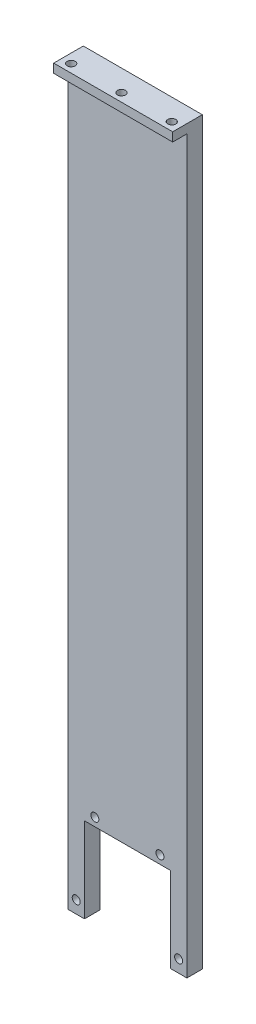
SolidWorks part; units mm, degrees
material "6061 Alloy"
ref_plane "Front Plane" through (0, 0, 0) normal (0, 0, 1) x (1, 0, 0)
ref_plane "Top Plane" through (0, 0, 0) normal (0, 1, 0) x (1, 0, 0)
ref_plane "Right Plane" through (0, 0, 0) normal (1, 0, 0) x (0, 0, -1)
sketch "Sketch1" plane through (0, 0, 0) normal (0, 0, 1) x (1, 0, 0)
  line L1 (-20.1, -125) -> (20.1, -125)
  line L2 (-20.1, -125) -> (-20.1, 125)
  line L3 (-20.1, 125) -> (20.1, 125)
  line L4 (20.1, -125) -> (20.1, 125)
  line L5 (-20.1, -125) -> (20.1, 125) construction
  line L6 (-20.1, 125) -> (20.1, -125) construction
  point P0 (0, 0)
  dimension "D1" = 40.2
  dimension "D2" = 250
extrude "Boss-Extrude1" add sketch "Sketch1" along normal blind 10
sketch "Sketch3" plane through (0, 0, 10) normal (0, 0, 1) x (1, 0, 0)
  line L0 (-20.1, -125) -> (20.1, -125) construction
  line L1 (-14.5, -96.3) -> (14.5, -96.3)
  line L2 (-14.5, -96.3) -> (-14.5, -125)
  line L3 (-14.5, -125) -> (14.5, -125)
  line L4 (14.5, -96.3) -> (14.5, -125)
  line L5 (-14.5, -96.3) -> (14.5, -125) construction
  line L6 (-14.5, -125) -> (14.5, -96.3) construction
  point P0 (0, -110.65)
  dimension "D1" = 29
  dimension "D2" = 28.7
sketch "Sketch2" plane through (0, 0, 10) normal (0, 0, 1) x (1, 0, 0)
  line L2 (-11, -93.5) -> (11, -93.5) construction
  line L3 (-17.3, -93.5) -> (17.3, -93.5) construction
  line L4 (-17.3, -93.5) -> (-17.3, -120.8) construction
  line L5 (-17.3, -120.8) -> (17.3, -120.8) construction
  line L6 (17.3, -93.5) -> (17.3, -120.8) construction
  line L7 (-17.3, -93.5) -> (17.3, -120.8) construction
  line L8 (-17.3, -120.8) -> (17.3, -93.5) construction
  line L9 (-20.1, -125) -> (20.1, -125) construction
  circle A0 centre (17.3, -120.8) radius 1.35
  circle A1 centre (11, -93.5) radius 1.35
  circle A2 centre (-17.3, -120.8) radius 1.35
  circle A3 centre (-11, -93.5) radius 1.35
  point P11 (0, -107.15)
  point P12 (0, -93.5)
  dimension "D1" = 4.2
  dimension "D2" = 2.7
  dimension "D3" = 22
  dimension "D4" = 27.3
  dimension "D5" = 34.6
sketch "Sketch4" plane through (0, 0, 10) normal (0, 0, 1) x (1, 0, 0)
  line L0 (-20.1, 125) -> (-20.1, -125) construction
  line L1 (-20.1, 122) -> (20.1, 122)
  line L2 (-20.1, 122) -> (-20.1, -125)
  line L3 (-20.1, -125) -> (20.1, -125)
  line L4 (20.1, 122) -> (20.1, -125)
  line L5 (-20.1, 122) -> (20.1, -125) construction
  line L6 (-20.1, -125) -> (20.1, 122) construction
  line L7 (20.1, 125) -> (-20.1, 125) construction
  point P0 (0, -1.5)
  dimension "D1" = 3
extrude "Cut-Extrude1" cut sketch "Sketch4" against normal blind 4.8
extrude "Cut-Extrude2" cut sketch "Sketch3" against normal through all
extrude "Cut-Extrude3" cut sketch "Sketch2" against normal through all
sketch "Sketch6" plane through (0, 125, 0) normal (0, 1, 0) x (-1, 0, 0)
  line L0 (17, 7.2) -> (-17, 7.2) construction
  line L2 (-20.1, 10) -> (20.1, 10) construction
  circle A0 centre (-17, 7.2) radius 1.35
  circle A1 centre (17, 7.2) radius 1.35
  circle A2 centre (0, 7.2) radius 1.35
  dimension "D1" = 2.7
  dimension "D2" = 17
  dimension "D3" = 2.8
extrude "Cut-Extrude4" cut sketch "Sketch6" against normal through all
